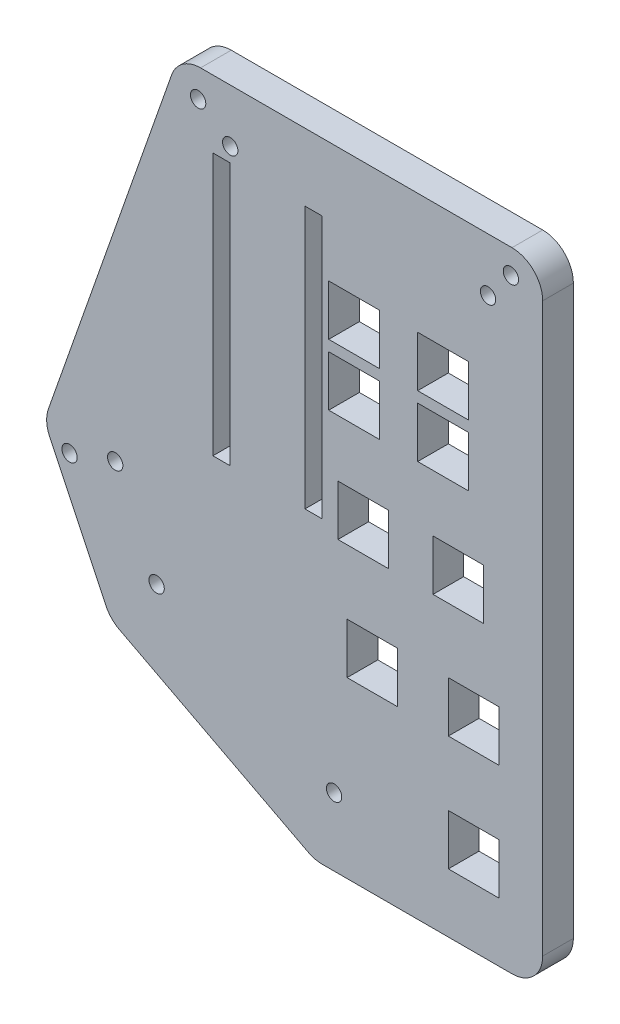
SolidWorks part; units mm, degrees
ref_plane "Front Plane" through (0, 0, 0) normal (0, 0, 1) x (1, 0, 0)
ref_plane "Top Plane" through (0, 0, 0) normal (0, 1, 0) x (1, 0, 0)
ref_plane "Right Plane" through (0, 0, 0) normal (1, 0, 0) x (0, 0, -1)
sketch "Sketch1" plane through (0, 0, 0) normal (0, 0, 1) x (1, 0, 0)
  line L6 (-20.066, -57.15) -> (46.99, -57.15) construction
  line L7 (-12.446, -73.152) -> (46.99, -73.152) construction
  line L8 (-3.3141, 6.35) -> (48.26, 6.35)
  line L9 (53.34, 1.27) -> (53.34, -92.71)
  line L10 (48.26, -97.79) -> (16.847, -97.79)
  line L16 (-8.1072, 2.9529) -> (-28.5162, -55.1739)
  line L18 (-20.066, -57.15) -> (-29.21, -57.15) construction
  line L26 (0, 0) -> (46.99, 0) construction
  line L27 (46.99, 0) -> (46.99, -88.9) construction
  line L28 (46.99, -88.9) -> (17.78, -88.9) construction
  line L29 (17.78, -88.9) -> (-12.446, -73.152) construction
  line L30 (-12.446, -73.152) -> (-20.066, -57.15) construction
  line L31 (-20.066, -57.15) -> (0, 0) construction
  line L32 (46.99, -57.15) -> (46.99, -88.9) construction
  line L33 (17.78, -88.9) -> (15.603, -97.79) construction
  line L34 (-12.446, -73.152) -> (-17.9301, -78.4424) construction
  line L35 (14.4997, -97.2152) -> (-16.7505, -80.9336)
  line L36 (-28.3096, -59.0409) -> (-18.9898, -78.6124)
  arc A0 (14.4997, -97.2152) -> (16.847, -97.79) centre (16.847, -92.71) ccw
  arc A1 (-28.5162, -55.1739) -> (-28.3096, -59.0409) centre (-23.723, -56.8568) ccw
  arc A2 (-16.7505, -80.9336) -> (-18.9898, -78.6124) centre (-14.4033, -76.4284) cw
  arc A3 (53.34, -92.71) -> (48.26, -97.79) centre (48.26, -92.71) cw
  arc A4 (48.26, 6.35) -> (53.34, 1.27) centre (48.26, 1.27) cw
  arc A5 (-8.1072, 2.9529) -> (-3.3141, 6.35) centre (-3.3141, 1.27) cw
  circle A6 centre (48.0822, 2.286) radius 1.27
  circle A7 centre (-3.7187, 1.651) radius 1.27
  circle A8 centre (-25.0123, -59.762) radius 1.27
  point P25 (53.34, -97.79)
  point P28 (53.34, 6.35)
  point P37 (0, 0)
  dimension "D11" = 5.2578
  dimension "D8" = 5.08
  dimension "D9" = 2.54
  dimension "D1" = 88.9
  dimension "D2" = 29.21
  dimension "D3" = 59.436
  dimension "D4" = 67.056
  dimension "D5" = 104.14
  dimension "D6" = 82.55
  dimension "D7" = 46.99
  dimension "D10" = 4.064
  dimension "D12" = 4.699
  dimension "D13" = 103.76
  dimension "D14" = 4.572
  dimension "D15" = 4.826
  dimension "D16" = 2.667
  dimension "D17" = 108.51
extrude "Boss-Extrude1" add sketch "Sketch1" along normal blind 5.08
sketch "Sketch3" plane through (0, 0, 5.08) normal (0, 0, 1) x (1, 0, 0)
  line L0 (46.99, -88.9) -> (0, -88.9) construction
  line L6 (-20.066, -57.15) -> (46.99, -57.15) construction
  line L7 (-12.446, -73.152) -> (46.99, -73.152) construction
  line L8 (0, 0) -> (46.99, 0) construction
  line L9 (46.99, 0) -> (46.99, -88.9) construction
  line L10 (46.99, -88.9) -> (17.78, -88.9) construction
  line L11 (17.78, -88.9) -> (-12.446, -73.152) construction
  line L12 (-12.446, -73.152) -> (-20.066, -57.15) construction
  line L13 (-20.066, -57.15) -> (0, 0) construction
sketch "Sketch5" plane through (0, 0, 0) normal (0, 0, -1) x (-1, 0, 0)
  line L0 (-46.99, 0) -> (-46.99, -17.78) construction
  line L1 (-46.99, 0) -> (-1.524, 0) construction
  line L2 (-46.99, -17.78) -> (-36.83, -17.78) construction
  line L3 (-46.99, 0) -> (-46.99, -27.94) construction
  line L8 (-41.021, -13.589) -> (-32.639, -13.589)
  line L9 (-41.021, -13.589) -> (-41.021, -21.971)
  line L10 (-46.99, 0) -> (-46.99, -45.72) construction
  line L15 (-41.021, -21.971) -> (-32.639, -21.971)
  line L16 (-32.639, -13.589) -> (-32.639, -21.971)
  line L17 (-46.99, 0) -> (-46.99, -88.9) construction
  line L18 (-46.99, -45.72) -> (-39.37, -45.72) construction
  line L19 (-41.021, -13.589) -> (-32.639, -21.971) construction
  line L20 (-46.99, 0) -> (-46.99, -64.77) construction
  line L21 (-43.561, -41.529) -> (-35.179, -41.529)
  line L22 (-43.561, -41.529) -> (-43.561, -49.911)
  line L23 (-43.561, -49.911) -> (-35.179, -49.911)
  line L24 (-35.179, -41.529) -> (-35.179, -49.911)
  line L25 (-43.561, -41.529) -> (-35.179, -49.911) construction
  line L26 (-43.561, -49.911) -> (-35.179, -41.529) construction
  line L27 (-46.99, -64.77) -> (-41.91, -64.77) construction
  line L28 (-41.021, -21.971) -> (-32.639, -13.589) construction
  line L29 (-46.99, -27.94) -> (-36.83, -27.94) construction
  line L30 (-46.99, 0) -> (-46.99, -83.82) construction
  line L31 (-41.021, -23.749) -> (-32.639, -23.749)
  line L32 (-41.021, -23.749) -> (-41.021, -32.131)
  line L33 (-41.021, -32.131) -> (-32.639, -32.131)
  line L34 (-32.639, -23.749) -> (-32.639, -32.131)
  line L35 (-41.021, -23.749) -> (-32.639, -32.131) construction
  line L36 (-41.021, -32.131) -> (-32.639, -23.749) construction
  line L37 (-46.101, -60.579) -> (-37.719, -60.579)
  line L38 (-46.101, -60.579) -> (-46.101, -68.961)
  line L39 (-46.101, -68.961) -> (-37.719, -68.961)
  line L40 (-37.719, -60.579) -> (-37.719, -68.961)
  line L41 (-46.101, -60.579) -> (-37.719, -68.961) construction
  line L42 (-46.101, -68.961) -> (-37.719, -60.579) construction
  line L43 (-46.99, -83.82) -> (-41.91, -83.82) construction
  line L44 (-36.83, -17.78) -> (-22.098, -17.78) construction
  line L45 (-46.101, -79.629) -> (-37.719, -79.629)
  line L46 (-46.101, -79.629) -> (-46.101, -88.011)
  line L47 (-46.101, -88.011) -> (-37.719, -88.011)
  line L48 (-37.719, -79.629) -> (-37.719, -88.011)
  line L49 (-46.101, -79.629) -> (-37.719, -88.011) construction
  line L50 (-46.101, -88.011) -> (-37.719, -79.629) construction
  line L51 (-36.83, -27.94) -> (-22.098, -27.94) construction
  line L52 (-39.37, -45.72) -> (-23.622, -45.72) construction
  line L53 (-41.91, -64.77) -> (-25.146, -64.77) construction
  line L54 (-46.99, 0) -> (-16.764, 0) construction
  line L55 (-26.289, -13.589) -> (-17.907, -13.589)
  line L56 (-26.289, -13.589) -> (-26.289, -21.971)
  line L57 (-26.289, -21.971) -> (-17.907, -21.971)
  line L58 (-17.907, -13.589) -> (-17.907, -21.971)
  line L59 (-26.289, -13.589) -> (-17.907, -21.971) construction
  line L60 (-26.289, -21.971) -> (-17.907, -13.589) construction
  line L61 (-26.289, -23.749) -> (-17.907, -23.749)
  line L62 (-26.289, -23.749) -> (-26.289, -32.131)
  line L63 (-26.289, -32.131) -> (-17.907, -32.131)
  line L64 (-17.907, -23.749) -> (-17.907, -32.131)
  line L65 (-26.289, -23.749) -> (-17.907, -32.131) construction
  line L66 (-26.289, -32.131) -> (-17.907, -23.749) construction
  line L67 (-27.813, -41.529) -> (-19.431, -41.529)
  line L68 (-27.813, -41.529) -> (-27.813, -49.911)
  line L69 (-27.813, -49.911) -> (-19.431, -49.911)
  line L70 (-19.431, -41.529) -> (-19.431, -49.911)
  line L71 (-27.813, -41.529) -> (-19.431, -49.911) construction
  line L72 (-27.813, -49.911) -> (-19.431, -41.529) construction
  line L73 (-29.337, -60.579) -> (-20.955, -60.579)
  line L74 (-29.337, -60.579) -> (-29.337, -68.961)
  line L75 (-29.337, -68.961) -> (-20.955, -68.961)
  line L76 (-20.955, -60.579) -> (-20.955, -68.961)
  line L77 (-29.337, -60.579) -> (-20.955, -68.961) construction
  line L78 (-29.337, -68.961) -> (-20.955, -60.579) construction
  line L79 (0, 0) -> (-46.99, 0) construction
  line L80 (-16.764, 0) -> (-16.764, -4.826) construction
  line L81 (-46.99, 0) -> (-13.97, 0) construction
  line L82 (-13.97, 0) -> (-13.97, -4.826) construction
  line L83 (-1.524, 0) -> (-1.524, -4.826) construction
  line L84 (-46.99, 0) -> (-17.1256, 0) construction
  line L85 (-1.524, 0) -> (-1.524, -48.26) construction
  line L86 (-46.99, 0) -> (1.27, 0) construction
  line L87 (1.27, 0) -> (1.27, -4.826) construction
  line L88 (-16.764, 0) -> (-16.764, -48.26) construction
  line L90 (-16.764, -4.826) -> (-13.97, -4.826)
  line L91 (-16.764, -4.826) -> (-16.764, -48.26)
  line L92 (-16.764, -48.26) -> (-13.97, -48.26)
  line L93 (-13.97, -4.826) -> (-13.97, -48.26)
  line L94 (-1.524, -4.826) -> (1.27, -4.826)
  line L95 (-1.524, -4.826) -> (-1.524, -48.26)
  line L96 (-1.524, -48.26) -> (1.27, -48.26)
  line L97 (1.27, -4.826) -> (1.27, -48.26)
  dimension "D2" = 8.382
  dimension "D3" = 64.77
  dimension "D4" = 8.382
  dimension "D5" = 10.16
  dimension "D6" = 17.78
  dimension "D7" = 8.382
  dimension "D8" = 8.382
  dimension "D9" = 45.72
  dimension "D10" = 7.62
  dimension "D11" = 8.382
  dimension "D12" = 8.382
  dimension "D13" = 27.94
  dimension "D14" = 10.16
  dimension "D15" = 5.08
  dimension "D16" = 8.382
  dimension "D17" = 8.382
  dimension "D18" = 8.382
  dimension "D19" = 8.382
  dimension "D20" = 83.82
  dimension "D21" = 5.08
  dimension "D22" = 8.382
  dimension "D23" = 8.382
  dimension "D24" = 14.732
  dimension "D25" = 8.382
  dimension "D26" = 8.382
  dimension "D27" = 14.732
  dimension "D28" = 8.382
  dimension "D29" = 8.382
  dimension "D30" = 15.748
  dimension "D31" = 8.382
  dimension "D32" = 8.382
  dimension "D33" = 16.764
  dimension "D34" = 30.226
  dimension "D35" = 4.826
  dimension "D36" = 33.02
  dimension "D37" = 4.826
  dimension "D38" = 45.466
  dimension "D39" = 4.826
  dimension "D40" = 48.26
  dimension "D41" = 4.826
  dimension "D42" = 48.26
  dimension "D43" = 48.26
extrude "Cut-Extrude1" cut sketch "Sketch5" against normal through all
sketch "Sketch7" plane through (0, 0, 5.08) normal (0, 0, 1) x (1, 0, 0)
  line L0 (46.99, 0) -> (44.2976, 0) construction
  line L1 (0, 0) -> (46.99, 0) construction
  line L2 (44.2976, 0) -> (44.2976, -2.4892) construction
  line L3 (46.99, 0) -> (1.6002, 0) construction
  line L4 (1.6002, 0) -> (1.6002, -2.4384) construction
  line L5 (-20.066, -57.15) -> (-17.4498, -57.15) construction
  line L6 (-20.066, -57.15) -> (46.99, -57.15) construction
  line L7 (-12.446, -73.152) -> (-10.5918, -73.152) construction
  line L8 (-12.446, -73.152) -> (46.99, -73.152) construction
  line L9 (-10.5918, -73.152) -> (-10.5918, -71.3486) construction
  line L10 (17.78, -88.9) -> (17.78, -86.5378) construction
  line L11 (17.78, -86.5378) -> (18.796, -86.5378) construction
  circle A0 centre (44.2976, -2.4892) radius 1.27
  circle A1 centre (1.6002, -2.4384) radius 1.27
  circle A2 centre (-17.4498, -57.15) radius 1.27
  circle A3 centre (-10.5918, -71.3486) radius 1.27
  circle A4 centre (18.796, -86.5378) radius 1.27
  dimension "D3" = 2.54
  dimension "D6" = 2.54
  dimension "D8" = 2.54
  dimension "D11" = 2.54
  dimension "D14" = 2.54
  dimension "D1" = 2.6924
  dimension "D2" = 2.4892
  dimension "D4" = 45.3898
  dimension "D5" = 2.4384
  dimension "D7" = 2.6162
  dimension "D9" = 1.8542
  dimension "D10" = 1.8034
  dimension "D12" = 2.3622
  dimension "D13" = 1.016
extrude "Cut-Extrude3" cut sketch "Sketch7" against normal through all
